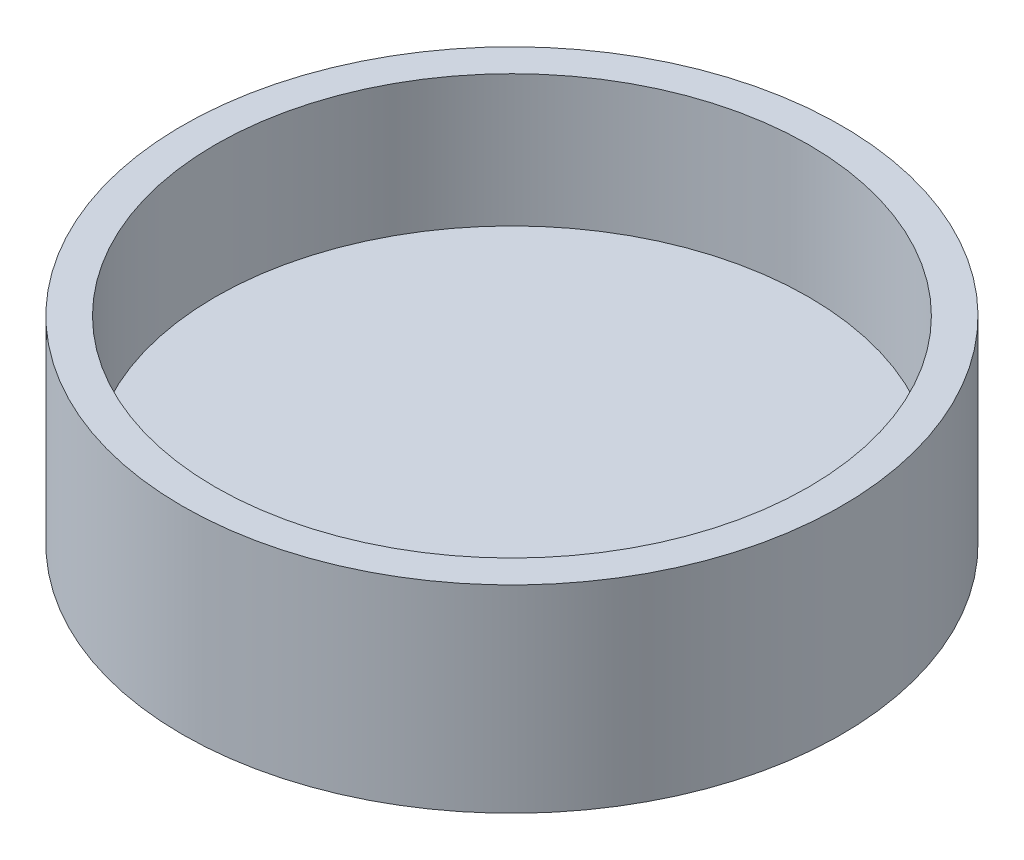
SolidWorks part; units mm, degrees
ref_plane "Plano frontal" through (0, 0, 0) normal (0, 0, 1) x (1, 0, 0)
ref_plane "Plano superior" through (0, 0, 0) normal (0, 1, 0) x (1, 0, 0)
ref_plane "Plano direito" through (0, 0, 0) normal (1, 0, 0) x (0, 0, -1)
sketch "Esboço1" plane through (0, 0, 0) normal (0, 1, 0) x (1, 0, 0)
  circle A0 centre (0, 0) radius 50
  dimension "D1" = 100
extrude "Ressalto-extrusão2" add sketch "Esboço1" along normal blind 10
sketch "Esboço2" plane through (0, 10, 0) normal (0, 1, 0) x (1, 0, 0)
  circle A0 centre (0, 0) radius 50
  circle A1 centre (0, 0) radius 45
  dimension "D1" = 90
extrude "Ressalto-extrusão4" add sketch "Esboço2" along normal blind 20
